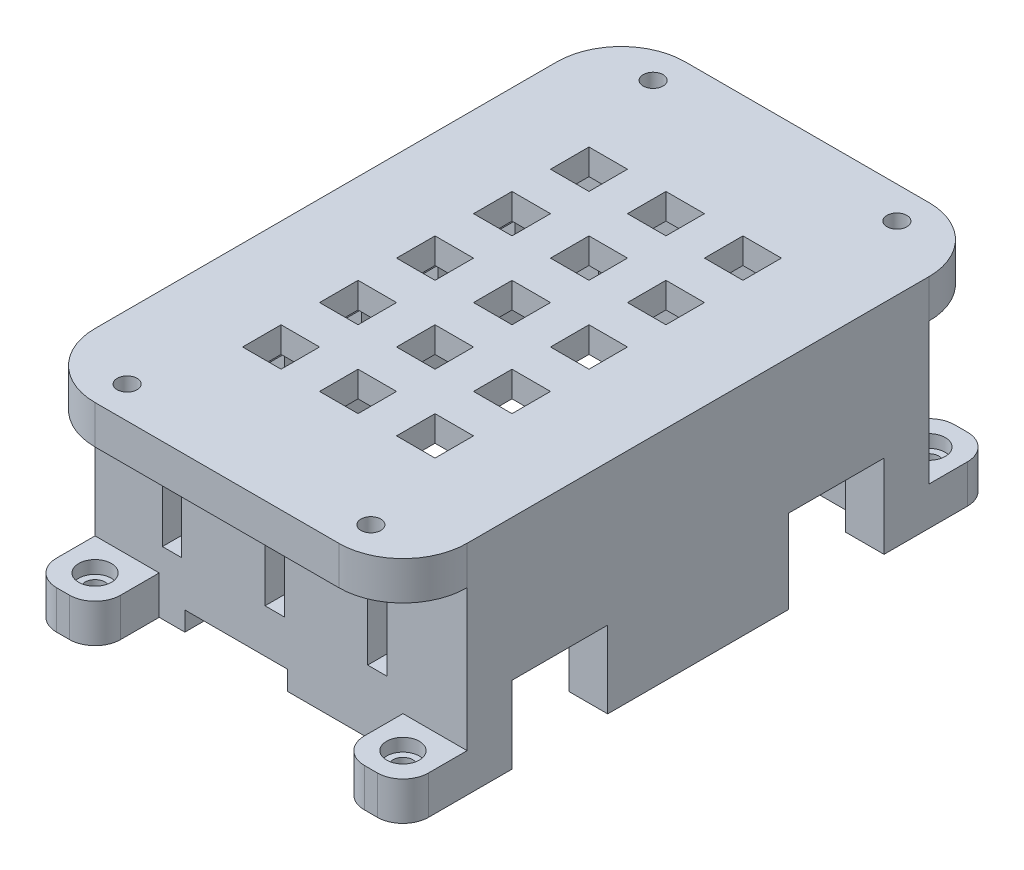
SolidWorks part; units mm, degrees
ref_plane "Спереди" through (0, 0, 0) normal (0, 0, 1) x (1, 0, 0)
ref_plane "Сверху" through (0, 0, 0) normal (0, 1, 0) x (1, 0, 0)
ref_plane "Справа" through (0, 0, 0) normal (1, 0, 0) x (0, 0, -1)
sketch "Sketch1" plane through (0, 0, 0) normal (0, 1, 0) x (1, 0, 0)
  line L1 (-13.5215, 25.3692) -> (11.4785, 25.3692)
  line L2 (-13.5215, 25.3692) -> (-13.5215, -6.6308)
  line L3 (-13.5215, -6.6308) -> (11.4785, -6.6308)
  line L4 (11.4785, 25.3692) -> (11.4785, -6.6308)
  dimension "D1" = 25
  dimension "D2" = 32
extrude "Boss-Extrude1" add sketch "Sketch1" along normal blind 2
sketch "Sketch2" plane through (0, 2, 0) normal (0, 1, 0) x (1, 0, 0)
  line L0 (11.4785, 25.3692) -> (-13.5215, 25.3692) construction
  line L1 (-15.5215, 27.3692) -> (13.4785, 27.3692)
  line L2 (-15.5215, 27.3692) -> (-15.5215, -8.6308)
  line L3 (-15.5215, -8.6308) -> (13.4785, -8.6308)
  line L4 (13.4785, 27.3692) -> (13.4785, -8.6308)
  line L5 (11.4785, -6.6308) -> (11.4785, 25.3692) construction
  line L6 (-13.5215, -6.6308) -> (11.4785, -6.6308) construction
  line L7 (-13.5215, 25.3692) -> (-13.5215, -6.6308) construction
  line L9 (-13.5215, 25.3692) -> (11.4785, 25.3692)
  line L10 (-13.5215, 25.3692) -> (-13.5215, -6.6308)
  line L11 (-13.5215, -6.6308) -> (11.4785, -6.6308)
  line L12 (11.4785, 25.3692) -> (11.4785, -6.6308)
  dimension "D1" = 2
  dimension "D2" = 2
  dimension "D3" = 2
  dimension "D4" = 2
extrude "Boss-Extrude2" add sketch "Sketch2" against normal blind 17
sketch "Sketch3" plane through (0, -15, 0) normal (0, -1, 0) x (1, 0, 0)
  line L0 (13.4785, -27.3692) -> (-15.5215, -27.3692) construction
  line L1 (-13.5215, -25.3692) -> (4.4785, -25.3692)
  line L2 (-13.5215, -25.3692) -> (-13.5215, -27.3692)
  line L3 (-13.5215, -27.3692) -> (4.4785, -27.3692)
  line L4 (4.4785, -25.3692) -> (4.4785, -27.3692)
  dimension "D1" = 18
extrude "Cut-Extrude1" cut sketch "Sketch3" against normal blind 2.7
sketch "Sketch4" plane through (0, -15, 0) normal (0, -1, 0) x (1, 0, 0)
  line L0 (-4.5215, -27.3692) -> (-4.5215, 8.6308) construction
  line L1 (-13.5215, -27.3692) -> (4.4785, -27.3692) construction
  line L2 (-15.5215, 8.6308) -> (13.4785, 8.6308) construction
  line L3 (-13.5215, 6.6308) -> (11.4785, 6.6308) construction
  line L4 (-8.5215, 8.6308) -> (-0.5215, 8.6308)
  line L5 (-8.5215, 8.6308) -> (-8.5215, 6.6308)
  line L6 (-8.5215, 6.6308) -> (-0.5215, 6.6308)
  line L7 (-0.5215, 8.6308) -> (-0.5215, 6.6308)
  dimension "D1" = 4
  dimension "D2" = 4
extrude "Cut-Extrude2" cut sketch "Sketch4" against normal blind 1.5
sketch "Sketch7" plane through (0, 0, 0) normal (0, -1, 0) x (1, 0, 0)
  line L0 (11.4785, -25.3692) -> (-13.5215, -25.3692) construction
  line L1 (11.4785, 6.6308) -> (10.4785, 6.6308)
  line L2 (11.4785, 6.6308) -> (11.4785, -25.3692)
  line L3 (11.4785, -25.3692) -> (10.4785, -25.3692)
  line L4 (10.4785, 6.6308) -> (10.4785, -25.3692)
  dimension "D1" = 1
extrude "Boss-Extrude3" add sketch "Sketch7" along normal blind 15
sketch "Sketch8" plane through (0, -15, 0) normal (0, -1, 0) x (1, 0, 0)
  line L0 (10.4785, 6.6308) -> (10.4785, -25.3692) construction
  line L1 (10.4785, 5.1308) -> (13.4785, 5.1308)
  line L2 (10.4785, 5.1308) -> (10.4785, -2.3292)
  line L3 (10.4785, -2.3292) -> (13.4785, -2.3292)
  line L4 (13.4785, 5.1308) -> (13.4785, -2.3292)
  line L5 (13.4785, 8.6308) -> (13.4785, -27.3692) construction
  line L6 (-0.5215, 6.6308) -> (10.4785, 6.6308) construction
  dimension "D1" = 7.46
  dimension "D2" = 1.5
extrude "Cut-Extrude4" cut sketch "Sketch8" against normal blind 6
sketch "Sketch9" plane through (0, -15, 0) normal (0, -1, 0) x (1, 0, 0)
  line L0 (13.4785, -2.3292) -> (13.4785, -27.3692) construction
  line L1 (13.4785, -23.8692) -> (10.4785, -23.8692)
  line L2 (13.4785, -23.8692) -> (13.4785, -16.4092)
  line L3 (13.4785, -16.4092) -> (10.4785, -16.4092)
  line L4 (10.4785, -23.8692) -> (10.4785, -16.4092)
  line L5 (10.4785, -2.3292) -> (10.4785, -25.3692) construction
  line L6 (10.4785, -25.3692) -> (4.4785, -25.3692) construction
  dimension "D1" = 7.46
  dimension "D2" = 1.5
extrude "Cut-Extrude5" cut sketch "Sketch9" against normal blind 6.5
sketch "Sketch10" plane through (0, 0, 8.6308) normal (0, 0, 1) x (1, 0, 0)
  line L0 (-15.5215, -15) -> (-15.5215, 2) construction
  line L1 (13.4785, 2) -> (-15.5215, 2)
  line L2 (13.4785, 2) -> (13.4785, -1)
  line L3 (13.4785, -1) -> (-15.5215, -1)
  line L4 (-15.5215, 2) -> (-15.5215, -1)
  dimension "D1" = 3
extrude "Boss-Extrude4" add sketch "Sketch10" along normal blind 5
sketch "Sketch11" plane through (0, 0, -27.3692) normal (0, 0, -1) x (-1, 0, 0)
  line L0 (15.5215, -15) -> (15.5215, 2) construction
  line L1 (-13.4785, 2) -> (15.5215, 2)
  line L2 (-13.4785, 2) -> (-13.4785, -1)
  line L3 (-13.4785, -1) -> (15.5215, -1)
  line L4 (15.5215, 2) -> (15.5215, -1)
  dimension "D1" = 3
extrude "Boss-Extrude5" add sketch "Sketch11" along normal blind 5
sketch "Sketch12" plane through (0, -1, 0) normal (0, -1, 0) x (1, 0, 0)
  line L0 (-15.5215, 13.6308) -> (-15.5215, 8.6308) construction
  line L1 (-15.5215, 13.6308) -> (13.4785, 13.6308) construction
  line L2 (13.4785, 13.6308) -> (13.4785, 8.6308) construction
  line L3 (-15.5215, -32.3692) -> (-15.5215, -27.3692) construction
  line L4 (13.4785, -32.3692) -> (-15.5215, -32.3692) construction
  line L5 (13.4785, -32.3692) -> (13.4785, -27.3692) construction
  circle A0 centre (-10.5215, 11.1308) radius 0.775
  circle A1 centre (8.4785, 11.1308) radius 0.775
  circle A2 centre (8.4785, -29.8692) radius 0.775
  circle A3 centre (-10.5215, -29.8692) radius 0.775
  dimension "D1" = 1.55
  dimension "D2" = 5
  dimension "D3" = 2.5
  dimension "D4" = 5
  dimension "D5" = 5
  dimension "D6" = 2.5
  dimension "D7" = 5
  dimension "D8" = 2.5
extrude "Cut-Extrude6" cut sketch "Sketch12" against normal through all
fillet "Fillet1" radius 5 4 edges at (-15.5215, 0.5, -32.3692) (13.4785, 0.5, -32.3692) (13.4785, 0.5, 13.6308) (-15.5215, 0.5, 13.6308)
sketch "Sketch13" plane through (0, -1, 0) normal (0, -1, 0) x (1, 0, 0)
  circle A0 centre (8.4785, -29.8692) radius 1.275
  circle A1 centre (-10.5215, -29.8692) radius 1.275
  circle A2 centre (8.4785, 11.1308) radius 1.275
  circle A3 centre (-10.5215, 11.1308) radius 1.275
  dimension "D1" = 2.55
extrude "Cut-Extrude7" cut sketch "Sketch13" against normal blind 1
sketch "Sketch14" plane through (0, 0, 8.6308) normal (0, 0, 1) x (1, 0, 0)
  line L1 (-15.5215, -15) -> (-10.5215, -15)
  line L2 (-15.5215, -15) -> (-15.5215, -12)
  line L3 (-15.5215, -12) -> (-10.5215, -12)
  line L4 (-10.5215, -15) -> (-10.5215, -12)
  line L5 (13.4785, -15) -> (8.4785, -15)
  line L6 (13.4785, -15) -> (13.4785, -12)
  line L7 (13.4785, -12) -> (8.4785, -12)
  line L8 (8.4785, -15) -> (8.4785, -12)
  dimension "D1" = 3
  dimension "D2" = 5
extrude "Boss-Extrude6" add sketch "Sketch14" along normal blind 5
sketch "Sketch15" plane through (0, 0, -27.3692) normal (0, 0, -1) x (-1, 0, 0)
  line L1 (-13.4785, -15) -> (-8.4785, -15)
  line L2 (-13.4785, -15) -> (-13.4785, -12)
  line L3 (-13.4785, -12) -> (-8.4785, -12)
  line L4 (-8.4785, -15) -> (-8.4785, -12)
  dimension "D1" = 3
  dimension "D2" = 5
extrude "Boss-Extrude7" add sketch "Sketch15" along normal blind 5
sketch "Sketch16" plane through (0, -15, 0) normal (0, -1, 0) x (1, 0, 0)
  line L0 (-15.5215, -27.3692) -> (-15.5215, 13.6308) construction
  line L1 (-15.5215, 13.6308) -> (-10.5215, 13.6308) construction
  line L2 (13.4785, 13.6308) -> (13.4785, 5.1308) construction
  line L4 (8.4785, 13.6308) -> (13.4785, 13.6308) construction
  line L5 (13.4785, -32.3692) -> (8.4785, -32.3692) construction
  line L6 (13.4785, -23.8692) -> (13.4785, -32.3692) construction
  circle A0 centre (10.9785, 11.1308) radius 0.775
  circle A1 centre (-13.0215, 11.1308) radius 0.775
  circle A2 centre (10.9785, -29.8692) radius 0.775
  dimension "D7" = 1.55
  dimension "D1" = 2.5
  dimension "D2" = 2.5
  dimension "D3" = 2.5
  dimension "D4" = 2.5
  dimension "D5" = 2.5
  dimension "D6" = 2.5
extrude "Cut-Extrude8" cut sketch "Sketch16" against normal blind 5
fillet "Fillet2" radius 2 6 edges at (13.4785, -13.5, 13.6308) (13.4785, -13.5, -32.3692) (8.4785, -13.5, -32.3692) (8.4785, -13.5, 13.6308) (-10.5215, -13.5, 13.6308) (-15.5215, -13.5, 13.6308)
sketch "Sketch17" plane through (0, -12, 0) normal (0, 1, 0) x (1, 0, 0)
  circle A0 centre (10.9785, -11.1308) radius 1.275
  circle A1 centre (-13.0215, -11.1308) radius 1.275
  circle A2 centre (10.9785, 29.8692) radius 1.275
  dimension "D1" = 2.55
extrude "Cut-Extrude9" cut sketch "Sketch17" against normal blind 1
sketch "Sketch18" plane through (0, 0, 8.6308) normal (0, 0, 1) x (1, 0, 0)
  line L0 (-2.2715, -10.0969) -> (-0.7715, -10.0969)
  line L1 (5.7285, -10.0969) -> (7.2285, -10.0969)
  line L2 (5.7285, -10.0969) -> (5.7285, -5.0969)
  line L3 (5.7285, -5.0969) -> (7.2285, -5.0969)
  line L4 (7.2285, -10.0969) -> (7.2285, -5.0969)
  line L5 (-2.2715, -10.0969) -> (-2.2715, -5.0969)
  line L6 (-2.2715, -5.0969) -> (-0.7715, -5.0969)
  line L7 (-0.7715, -10.0969) -> (-0.7715, -5.0969)
  line L8 (-10.2715, -10.0969) -> (-8.7715, -10.0969)
  line L9 (-10.2715, -10.0969) -> (-10.2715, -5.0969)
  line L10 (-10.2715, -5.0969) -> (-8.7715, -5.0969)
  line L11 (-8.7715, -10.0969) -> (-8.7715, -5.0969)
  line L12 (13.4785, -12) -> (13.4785, -1) construction
  dimension "D1" = 1.5
  dimension "D2" = 5
  dimension "D4" = 6.25
  dimension "D3" = 3
extrude "Cut-Extrude10" cut sketch "Sketch18" against normal through all
sketch "Sketch19" plane through (0, 2, 0) normal (0, 1, 0) x (1, 0, 0)
  line L0 (-2.5215, 22.8692) -> (0.4785, 22.8692)
  line L1 (-8.5215, 22.8692) -> (-5.5215, 22.8692)
  line L2 (-8.5215, 22.8692) -> (-8.5215, 19.8692)
  line L3 (-8.5215, 19.8692) -> (-5.5215, 19.8692)
  line L4 (-5.5215, 22.8692) -> (-5.5215, 19.8692)
  line L5 (0.4785, 22.8692) -> (0.4785, 19.8692)
  line L6 (-2.5215, 19.8692) -> (0.4785, 19.8692)
  line L7 (-2.5215, 22.8692) -> (-2.5215, 19.8692)
  line L8 (3.4785, 22.8692) -> (6.4785, 22.8692)
  line L9 (6.4785, 22.8692) -> (6.4785, 19.8692)
  line L10 (3.4785, 19.8692) -> (6.4785, 19.8692)
  line L11 (3.4785, 22.8692) -> (3.4785, 19.8692)
  line L12 (-2.5215, 16.8692) -> (0.4785, 16.8692)
  line L13 (0.4785, 16.8692) -> (0.4785, 13.8692)
  line L14 (-2.5215, 13.8692) -> (0.4785, 13.8692)
  line L15 (-2.5215, 16.8692) -> (-2.5215, 13.8692)
  line L16 (3.4785, 16.8692) -> (6.4785, 16.8692)
  line L17 (6.4785, 16.8692) -> (6.4785, 13.8692)
  line L18 (3.4785, 13.8692) -> (6.4785, 13.8692)
  line L19 (3.4785, 16.8692) -> (3.4785, 13.8692)
  line L20 (-2.5215, 10.8692) -> (0.4785, 10.8692)
  line L21 (0.4785, 10.8692) -> (0.4785, 7.8692)
  line L22 (-2.5215, 7.8692) -> (0.4785, 7.8692)
  line L23 (-2.5215, 10.8692) -> (-2.5215, 7.8692)
  line L24 (3.4785, 10.8692) -> (6.4785, 10.8692)
  line L25 (6.4785, 10.8692) -> (6.4785, 7.8692)
  line L26 (3.4785, 7.8692) -> (6.4785, 7.8692)
  line L27 (3.4785, 10.8692) -> (3.4785, 7.8692)
  line L28 (-2.5215, 4.8692) -> (0.4785, 4.8692)
  line L29 (0.4785, 4.8692) -> (0.4785, 1.8692)
  line L30 (-2.5215, 1.8692) -> (0.4785, 1.8692)
  line L31 (-2.5215, 4.8692) -> (-2.5215, 1.8692)
  line L32 (3.4785, 4.8692) -> (6.4785, 4.8692)
  line L33 (6.4785, 4.8692) -> (6.4785, 1.8692)
  line L34 (3.4785, 1.8692) -> (6.4785, 1.8692)
  line L35 (3.4785, 4.8692) -> (3.4785, 1.8692)
  line L36 (-2.5215, -1.1308) -> (0.4785, -1.1308)
  line L37 (0.4785, -1.1308) -> (0.4785, -4.1308)
  line L38 (-2.5215, -4.1308) -> (0.4785, -4.1308)
  line L39 (-2.5215, -1.1308) -> (-2.5215, -4.1308)
  line L40 (3.4785, -1.1308) -> (6.4785, -1.1308)
  line L41 (6.4785, -1.1308) -> (6.4785, -4.1308)
  line L42 (3.4785, -4.1308) -> (6.4785, -4.1308)
  line L43 (3.4785, -1.1308) -> (3.4785, -4.1308)
  line L44 (-8.5215, 16.8692) -> (-5.5215, 16.8692)
  line L45 (-5.5215, 16.8692) -> (-5.5215, 13.8692)
  line L46 (-8.5215, 13.8692) -> (-5.5215, 13.8692)
  line L47 (-8.5215, 16.8692) -> (-8.5215, 13.8692)
  line L48 (-8.5215, 10.8692) -> (-5.5215, 10.8692)
  line L49 (-5.5215, 10.8692) -> (-5.5215, 7.8692)
  line L50 (-8.5215, 7.8692) -> (-5.5215, 7.8692)
  line L51 (-8.5215, 10.8692) -> (-8.5215, 7.8692)
  line L52 (-8.5215, 4.8692) -> (-5.5215, 4.8692)
  line L53 (-5.5215, 4.8692) -> (-5.5215, 1.8692)
  line L54 (-8.5215, 1.8692) -> (-5.5215, 1.8692)
  line L55 (-8.5215, 4.8692) -> (-8.5215, 1.8692)
  line L56 (-8.5215, -1.1308) -> (-5.5215, -1.1308)
  line L57 (-5.5215, -1.1308) -> (-5.5215, -4.1308)
  line L58 (-8.5215, -4.1308) -> (-5.5215, -4.1308)
  line L59 (-8.5215, -1.1308) -> (-8.5215, -4.1308)
  line L60 (-10.5215, 32.3692) -> (8.4785, 32.3692) construction
  line L61 (-15.5215, 27.3692) -> (-15.5215, -8.6308) construction
  dimension "D1" = 3
  dimension "D2" = 3
  dimension "D5" = 9.5
  dimension "D6" = 7
  dimension "D3" = 3
  dimension "D4" = 5
extrude "Cut-Extrude11" cut sketch "Sketch19" against normal through all
sketch "Sketch21" plane through (-15.5215, 0, 0) normal (-1, 0, 0) x (0, 0, 1)
  line L0 (-27.3692, -15) -> (11.6308, -15) construction
  line L1 (3.3808, -10.1) -> (1.8808, -10.1)
  line L2 (3.3808, -10.1) -> (3.3808, -5.1)
  line L3 (3.3808, -5.1) -> (1.8808, -5.1)
  line L4 (1.8808, -10.1) -> (1.8808, -5.1)
  line L5 (-2.6192, -10.1) -> (-4.1192, -10.1)
  line L6 (-2.6192, -5.1) -> (-4.1192, -5.1)
  line L7 (-4.1192, -10.1) -> (-4.1192, -5.1)
  line L8 (-2.6192, -10.1) -> (-2.6192, -5.1)
  line L9 (-8.6192, -10.1) -> (-10.1192, -10.1)
  line L10 (-8.6192, -5.1) -> (-10.1192, -5.1)
  line L11 (-10.1192, -10.1) -> (-10.1192, -5.1)
  line L12 (-8.6192, -10.1) -> (-8.6192, -5.1)
  line L13 (-14.6192, -10.1) -> (-16.1192, -10.1)
  line L14 (-14.6192, -5.1) -> (-16.1192, -5.1)
  line L15 (-16.1192, -10.1) -> (-16.1192, -5.1)
  line L16 (-14.6192, -10.1) -> (-14.6192, -5.1)
  line L17 (-20.6192, -10.1) -> (-22.1192, -10.1)
  line L18 (-20.6192, -5.1) -> (-22.1192, -5.1)
  line L19 (-22.1192, -10.1) -> (-22.1192, -5.1)
  line L20 (-20.6192, -10.1) -> (-20.6192, -5.1)
  line L22 (8.6308, -12) -> (8.6308, -1) construction
  dimension "D1" = 5
  dimension "D2" = 1.5
  dimension "D3" = 4.9
  dimension "D5" = 5.25
  dimension "D4" = 5
extrude "Cut-Extrude12" cut sketch "Sketch21" against normal blind 2
